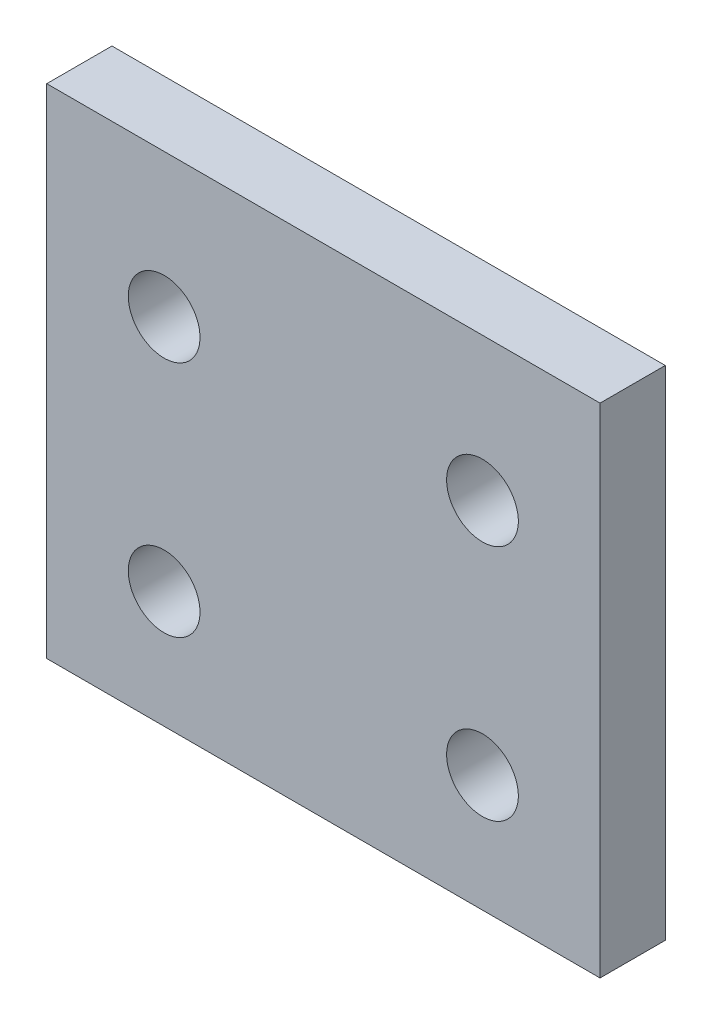
SolidWorks part; units mm, degrees
ref_plane "Front" through (0, 0, 0) normal (0, 0, 1) x (1, 0, 0)
ref_plane "Top" through (0, 0, 0) normal (0, 1, 0) x (1, 0, 0)
ref_plane "Right" through (0, 0, 0) normal (1, 0, 0) x (0, 0, -1)
sketch "Sketch1" plane through (0, 0, 0) normal (0, 0, 1) x (1, 0, 0)
  line L1 (0, 0) -> (21.2113, 0)
  line L2 (0, 0) -> (0, 19.086)
  line L3 (0, 19.086) -> (21.2113, 19.086)
  line L4 (21.2113, 0) -> (21.2113, 19.086)
  dimension "D1" = 19.086
  dimension "D2" = 21.2113
extrude "Boss-Extrude1" add sketch "Sketch1" along normal blind 2.5
sketch "Sketch2" plane through (0, 0, 0) normal (0, 0, -1) x (-1, 0, 0)
  line L0 (-21.2113, 19.086) -> (0, 19.086) construction
  line L1 (-21.2113, 0) -> (-21.2113, 19.086) construction
  circle A0 centre (-16.7032, 13.5977) radius 1.375
  circle A1 centre (-4.5006, 13.5977) radius 1.375
  circle A2 centre (-16.7032, 4.4801) radius 1.375
  circle A3 centre (-4.5006, 4.4801) radius 1.375
  dimension "D1" = 2.75
  dimension "D2" = 12.2026
  dimension "D3" = 9.1176
  dimension "D4" = 5.4883
  dimension "D5" = 4.5081
extrude "Cut-Extrude1" cut sketch "Sketch2" against normal through all
